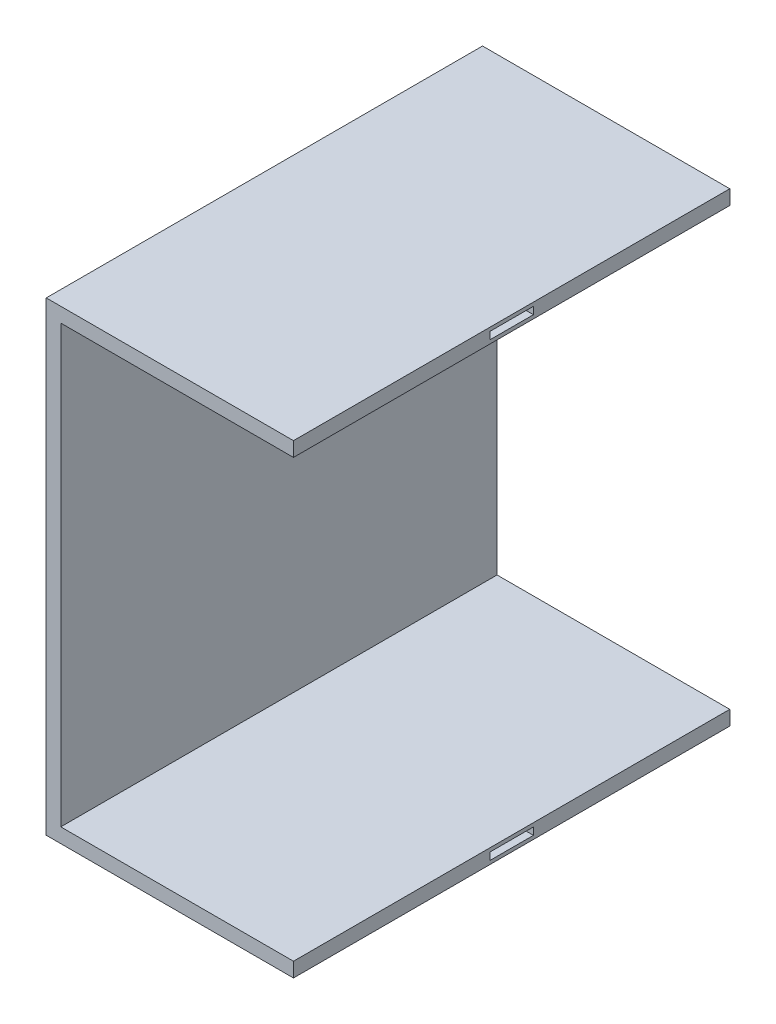
SolidWorks part; units mm, degrees
ref_plane "Front Plane" through (0, 0, 0) normal (0, 0, 1) x (1, 0, 0)
ref_plane "Top Plane" through (0, 0, 0) normal (0, 1, 0) x (1, 0, 0)
ref_plane "Right Plane" through (0, 0, 0) normal (1, 0, 0) x (0, 0, -1)
sketch "Sketch1" plane through (0, 0, 0) normal (0, 0, 1) x (1, 0, 0)
  line L0 (0, 0) -> (17, 0)
  line L1 (17, 0) -> (17, 1)
  line L2 (1, 1) -> (1, 31)
  line L3 (1, 31) -> (17, 31)
  line L4 (17, 31) -> (17, 32)
  line L5 (17, 32) -> (0, 32)
  line L6 (0, 32) -> (0, 0)
  line L7 (17, 1) -> (1, 1)
  dimension "D1" = 1
  dimension "D2" = 1
  dimension "D3" = 1
  dimension "D4" = 30
  dimension "D5" = 17
  dimension "D6" = 17
extrude "Boss-Extrude1" add sketch "Sketch1" along normal mid plane 30
sketch "Sketch2" plane through (17, 0, 0) normal (1, 0, 0) x (0, 0, -1)
  line L0 (15, 31) -> (15, 32) construction
  line L1 (-1.5, 31.75) -> (1.5, 31.75)
  line L2 (-1.5, 31.75) -> (-1.5, 31.25)
  line L3 (-1.5, 31.25) -> (1.5, 31.25)
  line L4 (1.5, 31.75) -> (1.5, 31.25)
  line L5 (-15, 31) -> (15, 31) construction
  dimension "D1" = 3
  dimension "D2" = 13.5
  dimension "D3" = 0.25
  dimension "D4" = 0.5
sketch "Sketch3" plane through (17, 0, 0) normal (1, 0, 0) x (0, 0, -1)
  line L0 (15, 0) -> (15, 1) construction
  line L1 (-1.5, 0.745) -> (1.5, 0.745)
  line L2 (-1.5, 0.745) -> (-1.5, 0.245)
  line L3 (-1.5, 0.245) -> (1.5, 0.245)
  line L4 (1.5, 0.745) -> (1.5, 0.245)
  line L5 (-15, 0) -> (15, 0) construction
  dimension "D1" = 3
  dimension "D2" = 13.5
  dimension "D3" = 0.245
  dimension "D4" = 0.5
extrude "Cut-Extrude1" cut sketch "Sketch3" against normal blind 1
extrude "Cut-Extrude2" cut sketch "Sketch2" against normal blind 1
sketch "Sketch5" plane through (0, 0, 0) normal (-1, 0, 0) x (0, 0, 1)
  line L1 (15, 0) -> (-15, 0) construction
  circle A0 centre (0, 16) radius 0.5
  dimension "D1" = 1
  dimension "D2" = 16
extrude "Cut-Extrude3" cut sketch "Sketch5" against normal mid plane 0.5
equation "\"mm\"=3.0531"
